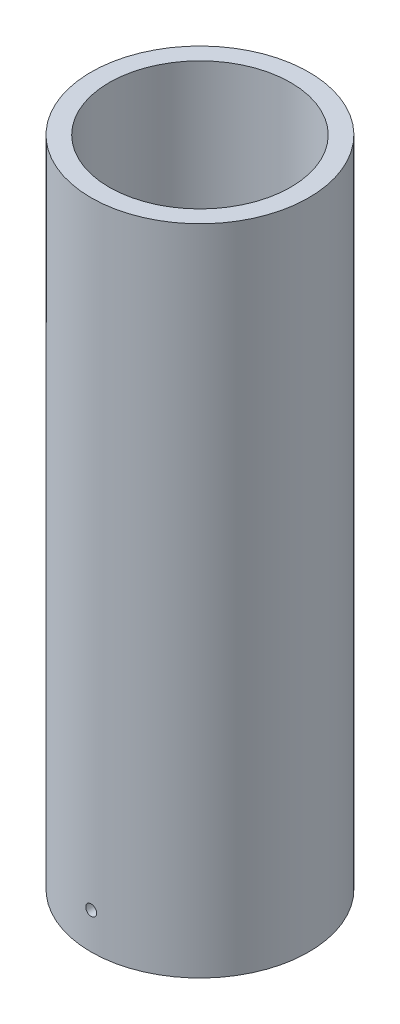
SolidWorks part; units mm, degrees
ref_plane "Front Plane" through (0, 0, 0) normal (0, 0, 1) x (1, 0, 0)
ref_plane "Top Plane" through (0, 0, 0) normal (0, 1, 0) x (1, 0, 0)
ref_plane "Right Plane" through (0, 0, 0) normal (1, 0, 0) x (0, 0, -1)
sketch "Sketch1" plane through (0, 0, 0) normal (0, 1, 0) x (1, 0, 0)
  circle A0 centre (0, 0) radius 30
  circle A1 centre (0, 0) radius 25
  dimension "D1" = 60
  dimension "D2" = 50
extrude "Boss-Extrude1" add sketch "Sketch1" along normal blind 180
sketch "Sketch2" plane through (0, 0, 0) normal (0, 0, 1) x (1, 0, 0)
  line L0 (0, 0) -> (0, 10) construction
  circle A0 centre (0, 10) radius 1.5
  dimension "D2" = 3
  dimension "D1" = 10
extrude "Cut-Extrude1" cut sketch "Sketch2" against normal through all and the other way through all
